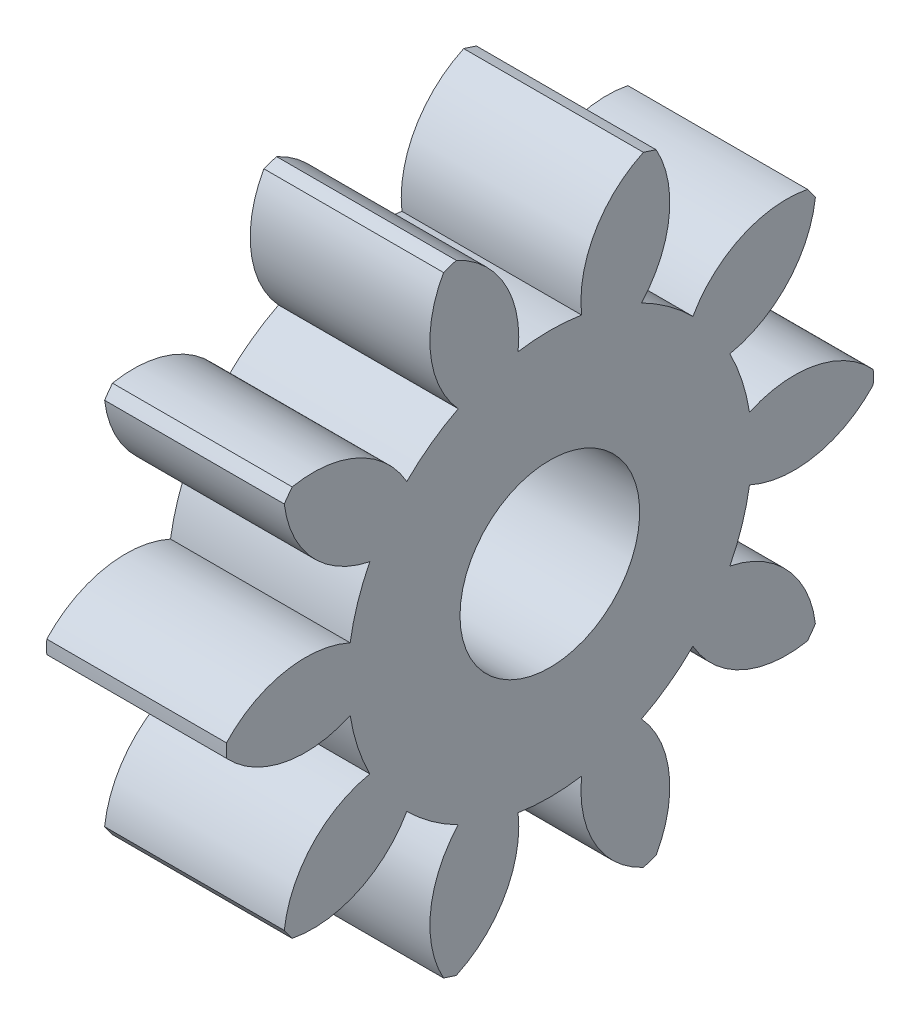
SolidWorks part; units mm, degrees
ref_plane "Plane1" through (0, 0, 0) normal (0, 0, 1) x (1, 0, 0)
ref_plane "Plane2" through (0, 0, 0) normal (0, 1, 0) x (1, 0, 0)
ref_plane "Plane3" through (0, 0, 0) normal (1, 0, 0) x (0, 0, -1)
sketch "HoldingSke" plane through (0, 0, 0) normal (0, 1, 0) x (1, 0, 0)
  line L0 (0, 0) -> (0.6565, -0.1158)
  line L1 (-15, 0) -> (100, 0) construction
  line L2 (0, 0) -> (-2.1039, 2.3779)
  line L3 (0, 0) -> (-11.863, 4.5341)
  line L4 (0, 0) -> (8.5048, 1.4996)
  line L5 (0, 0) -> (-46.8476, -17.4728)
  line L6 (0, 0) -> (-4.1448, -2.7965)
  line L7 (-2.1039, 2.3779) -> (8.6586, 51.2059)
  line L8 (-76.2, 54.61) -> (-75.3, 54.61)
  line L9 (-71.009, 38.7566) -> (-53.1078, 45.2721)
  line L10 (-76.2, 71.12) -> (104.1128, 71.12)
  line L11 (0, 0) -> (-5, 0)
  line L12 (-76.2, 101.6) -> (-76.147, 101.6)
  line L13 (24.9733, 27.94) -> (52.9518, 28.4284)
  line L14 (24.9733, 27.94) -> (24.9743, 27.94)
  line L15 (24.9733, 27.94) -> (100.4006, 29.5858)
  line L16 (-63.627, -1.5) -> (-12.827, -1.5)
  circle A0 centre (0, 0) radius 2.5
  circle A1 centre (0, 0) radius 5.624
  circle A2 centre (0, 0) radius 37.5
  circle A3 centre (0, 0) radius 2.5
  dimension "MHD" = 11.248
  dimension "Hub_dia" = 75
  dimension "Bore" = 5
  dimension "MBD" = 5
  dimension "Num_teeth" = 10
  dimension "Pitch_radius" = 180.3128
  dimension "Pitch" = 0.6667
  dimension "Width" = 5
  dimension "Overall_len" = 50
  dimension "Show_teeth" = 10
  dimension "Thickness" = 5
  dimension "OAL" = 50.0001
  dimension "T_dim" = 0.9
  dimension "Ap" = 20
  dimension "H" = 19.05
  dimension "Backlash" = 0.053
  dimension "Addendum_fac" = 1
  dimension "Dedendum_fac" = 1.25
  dimension "Clearance_fac" = 0.25
  dimension "Dedendum_add" = 0.001
  dimension "Module" = 1.5
sketch "BasProSke" plane through (0, 0, 0) normal (0, 1, 0) x (1, 0, 0)
  line L0 (-10, 0) -> (60, 0) construction
  line L1 (0, 0) -> (0, 9)
  line L2 (0, 0) -> (5, 0)
  line L3 (5, 0) -> (5, 9)
  line L4 (5, 9) -> (0, 9)
  dimension "Diameter" = 18
  dimension "Thickness" = 5
revolve "Base-Revolve" add sketch "BasProSke" angle 360 about L0
sketch "TooCutSke" plane through (0, 0, 0) normal (1, 0, 0) x (0, 0, -1)
  line L1 (0, 0) -> (0, 107) construction
  line L2 (0, 0) -> (-1.2658, 7.3924) construction
  line L3 (0, 0) -> (-4.5869, 14.117) construction
  line L4 (-1.2658, 7.3924) -> (-2.2934, 7.0585) construction
  arc A0 (0.8839, 5.5541) -> (-0.8839, 5.5541) centre (0, 0) ccw
  arc A1 (2.6378, 8.6313) -> (-2.6378, 8.6313) centre (0, 0) ccw
  circle A2 centre (0, 0) radius 7.5 construction
  circle A3 centre (0, 0) radius 7.0477 construction
  arc A4 (-0.8839, 5.5541) -> (-2.6378, 8.6313) centre (-3.8646, 5.8936) ccw
  arc A5 (2.6378, 8.6313) -> (0.8839, 5.5541) centre (3.8646, 5.8936) ccw
  dimension "Root_dia" = 11.248
  dimension "Overcut_dia" = 18.0508
  dimension "Pitch_dia" = 15
  dimension "Base_dia" = 14.0954
  dimension "Flank_rad" = 3
  dimension "Half_ang" = 18
  dimension "Half_CT" = 1.0805
extrude "ToothCut" cut sketch "TooCutSke" along normal through all
fillet "Breaks" [suppressed] radius 0.03
fillet "RootFillets" [suppressed] radius 0.376
pattern_circular "TeethCuts" count 10 every 36 about axis through (-10, 0, 0) along (1, 0, 0) of "ToothCut", "RootFillets", "Breaks"
sketch "HubNeaOneSke" plane through (0, 0, 0) normal (-1, 0, 0) x (0, 0, 1)
  circle A0 centre (0, 0) radius 5.624
  dimension "Diameter" = 11.248
extrude "HubNearOne" [suppressed] add sketch "HubNeaOneSke" along normal blind 45.0001
sketch "HubNeaBotSke" plane through (0, 0, 0) normal (-1, 0, 0) x (0, 0, 1)
  circle A0 centre (0, 0) radius 5.624
  dimension "Diameter" = 11.248
extrude "HubNearBoth" [suppressed] add sketch "HubNeaBotSke" along normal blind 22.5
ref_plane "FarPln" through (5, 0, 0) normal (1, 0, 0) x (0, 0, -1)
sketch "HubFarSke" plane through (5, 0, 0) normal (1, 0, 0) x (0, 0, -1)
  circle A0 centre (0, 0) radius 5.624
  dimension "Diameter" = 11.248
extrude "HubFar" [suppressed] add sketch "HubFarSke" along normal blind 22.5
sketch "BorSke" plane through (0, 0, 0) normal (1, 0, 0) x (0, 0, -1)
  circle A0 centre (0, 0) radius 2.5
  dimension "Diameter" = 5
extrude "Bore" cut sketch "BorSke" along normal mid plane 100.0001
sketch "KeySke" plane through (0, 0, 0) normal (1, 0, 0) x (0, 0, -1)
  line L0 (-1, 0) -> (-1, 3.4)
  line L1 (-1, 3.4) -> (1, 3.4)
  line L2 (1, 3.4) -> (1, 0)
  line L3 (0, 0) -> (0, 34) construction
  line L4 (-1, 0) -> (1, 0)
  dimension "Offset" = 3.4
  dimension "Width" = 2
extrude "Keyway" [suppressed] cut sketch "KeySke" along normal mid plane 100.0001
pattern_circular "Keyway2" [suppressed] count 2 every 90 about axis through (-10, 0, 0) along (1, 0, 0)
equation "' \"Module@HoldingSke\" = 6.35"
equation "' \"Num_teeth@HoldingSke\" = 12"
equation "' \"Ap@HoldingSke\" =  20"
equation "' \"Width@HoldingSke\" = 0.5 * 25.4"
equation "' \"Hub_dia@HoldingSke\"= 1 * 25.4"
equation "' \"Overall_len@HoldingSke\" = 1.0 * 25.4"
equation "' \"Bore@HoldingSke\" = 0.75 * 25.4"
equation "' \"T_dim@HoldingSke\" = 0.1 * 25.4"
equation "' \"Width@KeySke\" = 0.25 * 25.4"
equation "' \"Show_teeth@HoldingSke\" = 13"
equation "' \"Backlash@HoldingSke\" = 0.009 * 25.4"
equation "' \"Addendum_fac@HoldingSke\" = 1.0"
equation "' \"Dedendum_fac@HoldingSke\" = 1.25"
equation "' \"Dedendum_add@HoldingSke\" = 0.00005 * 25.4"
equation "' \"Clearance_fac@HoldingSke\" = 0.25"
equation "\"Pitch@HoldingSke\" = 1 / \"Module@HoldingSke\""
equation "\"Overcut_dia@TooCutSke\" = (\"Num_teeth@HoldingSke\" + 2 * \"Addendum_fac@HoldingSke\") / \"Pitch@HoldingSke\" + 0.002 * 25.4"
equation "\"Pitch_dia@TooCutSke\" = \"Num_teeth@HoldingSke\" / \"Pitch@HoldingSke\""
equation "\"Base_dia@TooCutSke\" = \"Num_teeth@HoldingSke\" / \"Pitch@HoldingSke\" * cos((\"Ap@HoldingSke\"  * 3.14159265 / 180))"
equation "\"Root_dia@TooCutSke\" = (\"Num_teeth@HoldingSke\" + 2) / \"Pitch@HoldingSke\" - 2 * (\"Addendum_fac@HoldingSke\" + \"Dedendum_fac@HoldingSke\") / \"Pitch@HoldingSke\" - \"Dedendum_add@HoldingSke\" * 2"
equation "\"Half_ang@TooCutSke\" = 180 / \"Num_teeth@HoldingSke\""
equation "\"Half_CT@TooCutSke\" = \"Num_teeth@HoldingSke\" / \"Pitch@HoldingSke\" * sin((3.14159265 / 2 / \"Num_teeth@HoldingSke\")) / 2 - 7 * \"Backlash@HoldingSke\" / 4"
equation "\"Flank_rad@TooCutSke\" = \"Num_teeth@HoldingSke\" / \"Pitch@HoldingSke\" / 5"
equation "\"Radius@RootFillets\" = \"Clearance_fac@HoldingSke\" / \"Pitch@HoldingSke\" + \"Dedendum_add@HoldingSke\""
equation "\"Break_rad@Breaks\" = 0.02 / \"Pitch@HoldingSke\""
equation "\"Thickness@HoldingSke\" = \"Width@HoldingSke\""
equation "\"OAL@HoldingSke\" = \"Thickness@HoldingSke\""
equation "\"MHD@HoldingSke\" = (\"Num_teeth@HoldingSke\" + 2) / \"Pitch@HoldingSke\" - 2 * (\"Addendum_fac@HoldingSke\" + \"Dedendum_fac@HoldingSke\")  / \"Pitch@HoldingSke\" - \"Dedendum_add@HoldingSke\" * 2"
equation "\"MBD@HoldingSke\" = (\"Num_teeth@HoldingSke\" + 2) / \"Pitch@HoldingSke\" - 2 * (\"Addendum_fac@HoldingSke\" + \"Dedendum_fac@HoldingSke\")  / \"Pitch@HoldingSke\" - \"Dedendum_add@HoldingSke\" * 2 - 0.002 * 25.4"
equation "\"MHD@HoldingSke\" = ((sgn( \"MHD@HoldingSke\" - \"Hub_dia@HoldingSke\" )-1)*( \"MHD@HoldingSke\" - \"Hub_dia@HoldingSke\" ))/-2+ \"Hub_dia@HoldingSke\""
equation "\"MBD@HoldingSke\" = ((sgn( \"MBD@HoldingSke\" - \"Bore@HoldingSke\" )-1)*( \"MBD@HoldingSke\" - \"Bore@HoldingSke\" ))/-2+ \"Bore@HoldingSke\""
equation "\"OAL@HoldingSke\" = ((sgn( \"OAL@HoldingSke\" - \"Overall_len@HoldingSke\" )+1)*( \"OAL@HoldingSke\" - \"Overall_len@HoldingSke\" ))/2 + \"Overall_len@HoldingSke\" + 0.000002 * 25.4"
equation "\"Num_teeth@TeethCuts\" = int( \"Show_teeth@HoldingSke\" ) + 1"
equation "\"Num_teeth@TeethCuts\" = ((sgn( \"Num_teeth@TeethCuts\" - \"Num_teeth@HoldingSke\" )-1)*( \"Num_teeth@TeethCuts\" - \"Num_teeth@HoldingSke\" ))/-2+ \"Num_teeth@HoldingSke\""
equation "\"Num_teeth@TeethCuts\" = ((sgn( \"Num_teeth@TeethCuts\" - 2.0)+1)*( \"Num_teeth@TeethCuts\" - 2.0))/2 +2.0"
equation "\"Angle@TeethCuts\" = 360.0 / \"Num_teeth@HoldingSke\""
equation "\"Diameter@BasProSke\" = (\"Num_teeth@HoldingSke\" + 2 * \"Addendum_fac@HoldingSke\") / \"Pitch@HoldingSke\""
equation "\"Thickness@BasProSke\"  = \"Thickness@HoldingSke\""
equation "' \"Fillet_rad@BasProSke\" =  \"Thickness@HoldingSke\" * 0.05"
equation "\"MHD@HoldingSke\" = ((sgn( \"MHD@HoldingSke\" - \"Root_dia@TooCutSke\" )-1)*( \"MHD@HoldingSke\" - \"Root_dia@TooCutSke\" ))/-2+ \"Root_dia@TooCutSke\""
equation "\"Diameter@HubNeaOneSke\" = \"MHD@HoldingSke\""
equation "\"Length@HubNearOne\" = \"OAL@HoldingSke\" - \"Thickness@BasProSke\""
equation "\"Diameter@HubNeaBotSke\" = \"MHD@HoldingSke\""
equation "\"Length@HubNearBoth\" = ( \"OAL@HoldingSke\" - \"Thickness@BasProSke\" ) / 2.0"
equation "\"Thickness@FarPln\" = \"Thickness@BasProSke\""
equation "\"Diameter@HubFarSke\" = \"MHD@HoldingSke\""
equation "\"Length@HubFar\" = ( \"OAL@HoldingSke\" - \"Thickness@BasProSke\" ) / 2.0"
equation "\"Diameter@BorSke\" = \"MBD@HoldingSke\""
equation "\"D1@Bore\" = \"OAL@HoldingSke\" * 2.0"
equation "\"D1@Keyway\" = \"OAL@HoldingSke\" * 2.0"
equation "\"Offset@KeySke\" = \"T_dim@HoldingSke\" + \"MBD@HoldingSke\" / 2.0"
